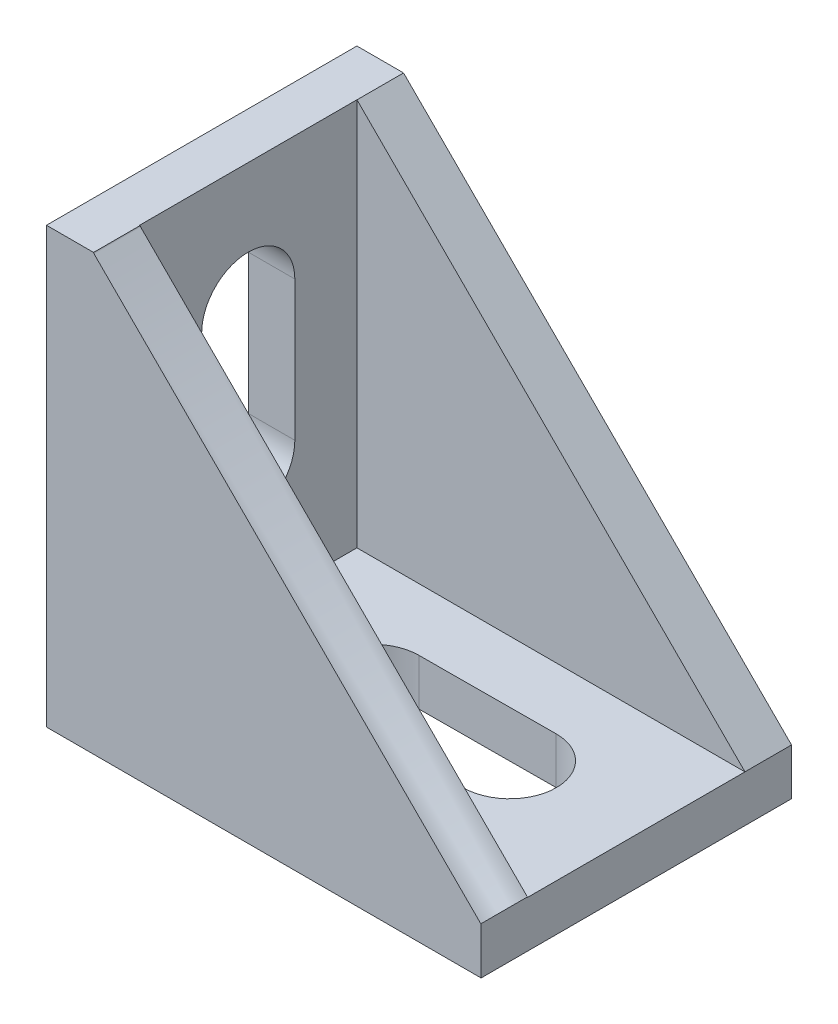
SolidWorks part; units mm, degrees
ref_plane "Front Plane" through (0, 0, 0) normal (0, 0, 1) x (1, 0, 0)
ref_plane "Top Plane" through (0, 0, 0) normal (0, 1, 0) x (1, 0, 0)
ref_plane "Right Plane" through (0, 0, 0) normal (1, 0, 0) x (0, 0, -1)
sketch "Sketch1" plane through (0, 0, 0) normal (0, 1, 0) x (1, 0, 0)
  line L1 (-13.1748, 12.2378) -> (14.8252, 12.2378)
  line L2 (-13.1748, 12.2378) -> (-13.1748, -7.7622)
  line L3 (-13.1748, -7.7622) -> (14.8252, -7.7622)
  line L4 (14.8252, 12.2378) -> (14.8252, -7.7622)
  line L5 (-13.1748, 12.2378) -> (14.8252, -7.7622) construction
  line L6 (-13.1748, -7.7622) -> (14.8252, 12.2378) construction
  point P4 (0.8252, 2.2378)
  dimension "D1" = 20
  dimension "D2" = 28
extrude "Boss-Extrude1" add sketch "Sketch1" along normal blind 3
sketch "Sketch2" plane through (0, 3, 0) normal (0, 1, 0) x (1, 0, 0)
  line L0 (-13.1748, -7.7622) -> (14.8252, -7.7622) construction
  line L1 (-13.1748, 12.2378) -> (-10.1748, 12.2378)
  line L2 (-13.1748, 12.2378) -> (-13.1748, -7.7622)
  line L3 (-13.1748, -7.7622) -> (-10.1748, -7.7622)
  line L4 (-10.1748, 12.2378) -> (-10.1748, -7.7622)
  line L5 (-13.1748, 12.2378) -> (-10.1748, -7.7622) construction
  line L6 (-13.1748, -7.7622) -> (-10.1748, 12.2378) construction
  point P4 (-11.6748, 2.2378)
extrude "Boss-Extrude2" add sketch "Sketch2" along normal blind 25
sketch "Sketch3" plane through (0, 3, 0) normal (0, 1, 0) x (1, 0, 0)
  line L0 (-10.1748, -7.7622) -> (-10.1748, 12.2378) construction
  line L1 (14.8252, -7.7622) -> (-10.1748, -7.7622)
  line L2 (14.8252, -7.7622) -> (14.8252, -4.7622)
  line L3 (14.8252, -4.7622) -> (-10.1748, -4.7622)
  line L4 (-10.1748, -7.7622) -> (-10.1748, -4.7622)
  line L5 (14.8252, -7.7622) -> (-10.1748, -4.7622) construction
  line L6 (14.8252, -4.7622) -> (-10.1748, -7.7622) construction
  line L8 (14.8252, 12.2378) -> (-10.1748, 12.2378)
  line L9 (14.8252, 12.2378) -> (14.8252, 9.2378)
  line L10 (14.8252, 9.2378) -> (-10.1748, 9.2378)
  line L11 (-10.1748, 12.2378) -> (-10.1748, 9.2378)
  line L12 (14.8252, 12.2378) -> (-10.1748, 9.2378) construction
  line L13 (14.8252, 9.2378) -> (-10.1748, 12.2378) construction
  point P4 (2.3252, -6.2622)
  point P12 (2.3252, 10.7378)
extrude "Boss-Extrude3" add sketch "Sketch3" along normal blind 25
sketch "Sketch4" plane through (0, 0, -9.2378) normal (0, 0, 1) x (1, 0, 0)
  spline S0 degree 3 poles (14.8164, 3.0088) (6.4879, 11.3373) (-1.8406, 19.6657) (-10.169, 27.9942) (-10.1696, 27.9948) (-10.1709, 27.9961) (-10.1705, 28.0013) (-10.1688, 28.0017) (-10.168, 28.002) (-0.3493, 30.847) (9.4694, 33.692) (19.2881, 36.537) (19.2893, 36.5374) (19.2919, 36.5381) (19.2978, 36.5346) (19.298, 36.532) (19.2981, 36.5307) (19.9552, 27.0954) (20.6124, 17.6601) (21.2696, 8.2248) (21.2699, 8.2205) (21.2705, 8.2119) (21.2641, 8.1974) (21.2575, 8.192) (21.2541, 8.1893) (19.1144, 6.4622) (16.9746, 4.735) (14.8349, 3.0078) (14.8333, 3.0065) (14.8301, 3.0039) (14.8207, 3.0044) (14.8178, 3.0074) (14.8164, 3.0088) (6.4879, 11.3373) (-1.8406, 19.6657) knots -0.00006 0 0 0 0.344046 0.344046 0.344046 0.344072 0.344097 0.344123 0.344123 0.344123 0.642727 0.642727 0.642727 0.642766 0.642804 0.642843 0.642843 0.642843 0.919119 0.919119 0.919119 0.919245 0.91937 0.919496 0.919496 0.919496 0.99982 0.99982 0.99982 0.99988 0.99994 1 1 1 1.344046 1.344046 1.344046 only from (14.8164, 3.0088) to (14.8164, 3.0088)
extrude "Cut-Extrude1" cut sketch "Sketch4" against normal blind 25
sketch "Sketch5" plane through (0, 0, 4.7622) normal (0, 0, -1) x (-1, 0, 0)
  spline S0 degree 3 poles (-35.0673, 33.9612) (-29.391, 36.1785) (-23.7148, 38.3957) (-18.0386, 40.613) (-17.9638, 40.6422) (-17.8142, 40.7007) (-17.5591, 40.7182) (-17.3995, 40.6992) (-17.3198, 40.6897) (-10.2094, 39.8438) (-3.0989, 38.9979) (4.0115, 38.152) (4.0465, 38.1478) (4.1164, 38.1395) (4.2232, 38.0698) (4.2591, 38.0092) (4.277, 37.9789) (6.2242, 34.6843) (8.1714, 31.3896) (10.1187, 28.095) (10.1285, 28.0783) (10.1483, 28.045) (10.1379, 27.9631) (10.1105, 27.9357) (10.0968, 27.922) (1.8098, 19.635) (-6.4771, 11.348) (-14.7641, 3.0611) (-14.7737, 3.0515) (-14.7929, 3.0323) (-14.8575, 3.0323) (-14.8767, 3.0515) (-14.8863, 3.0611) (-16.6309, 4.8057) (-18.3755, 6.5503) (-20.1201, 8.2949) (-20.2292, 8.404) (-20.4474, 8.6222) (-20.734, 8.9957) (-20.8884, 9.263) (-20.9656, 9.3966) (-25.677, 17.5538) (-30.3884, 25.711) (-35.0999, 33.8682) (-35.1054, 33.8777) (-35.1163, 33.8966) (-35.0979, 33.9493) (-35.0775, 33.9572) (-35.0673, 33.9612) (-29.391, 36.1785) (-23.7148, 38.3957) knots -0.000263 0 0 0 0.146384 0.146384 0.146384 0.148313 0.150243 0.152172 0.152172 0.152172 0.324179 0.324179 0.324179 0.325025 0.325871 0.326717 0.326717 0.326717 0.418647 0.418647 0.418647 0.419113 0.419579 0.420044 0.420044 0.420044 0.701563 0.701563 0.701563 0.701889 0.702215 0.702542 0.702542 0.702542 0.761808 0.761808 0.761808 0.765515 0.769221 0.772928 0.772928 0.772928 0.999211 0.999211 0.999211 0.999474 0.999737 1 1 1 1.146384 1.146384 1.146384 only from (-35.0673, 33.9612) to (-35.0673, 33.9612)
extrude "Cut-Extrude2" cut sketch "Sketch5" against normal blind 25
sketch "Sketch6" plane through (-10.1748, 0, 0) normal (1, 0, 0) x (0, 0, -1)
  line L4 (2.2378, 11) -> (2.2378, 20) construction
  line L5 (-0.7622, 11) -> (-0.7622, 20)
  line L6 (5.2378, 11) -> (5.2378, 20)
  arc A0 (-0.7622, 11) -> (5.2378, 11) centre (2.2378, 11) ccw
  arc A1 (5.2378, 20) -> (-0.7622, 20) centre (2.2378, 20) ccw
  point P8 (2.2378, 15.5)
extrude "Cut-Extrude3" cut sketch "Sketch6" against normal blind 25
sketch "Sketch7" plane through (0, 3, 0) normal (0, 1, 0) x (1, 0, 0)
  line L3 (6.6296, 2.2796) -> (-2.1748, 2.2378) construction
  line L4 (6.6438, -0.7204) -> (-2.1606, -0.7622)
  line L5 (6.6153, 5.2796) -> (-2.1891, 5.2377)
  arc A0 (6.6438, -0.7204) -> (6.6153, 5.2796) centre (6.6296, 2.2796) ccw
  arc A1 (-2.1891, 5.2377) -> (-2.1606, -0.7622) centre (-2.1748, 2.2378) ccw
  point P6 (2.2274, 2.2587)
extrude "Cut-Extrude4" cut sketch "Sketch7" against normal blind 25
